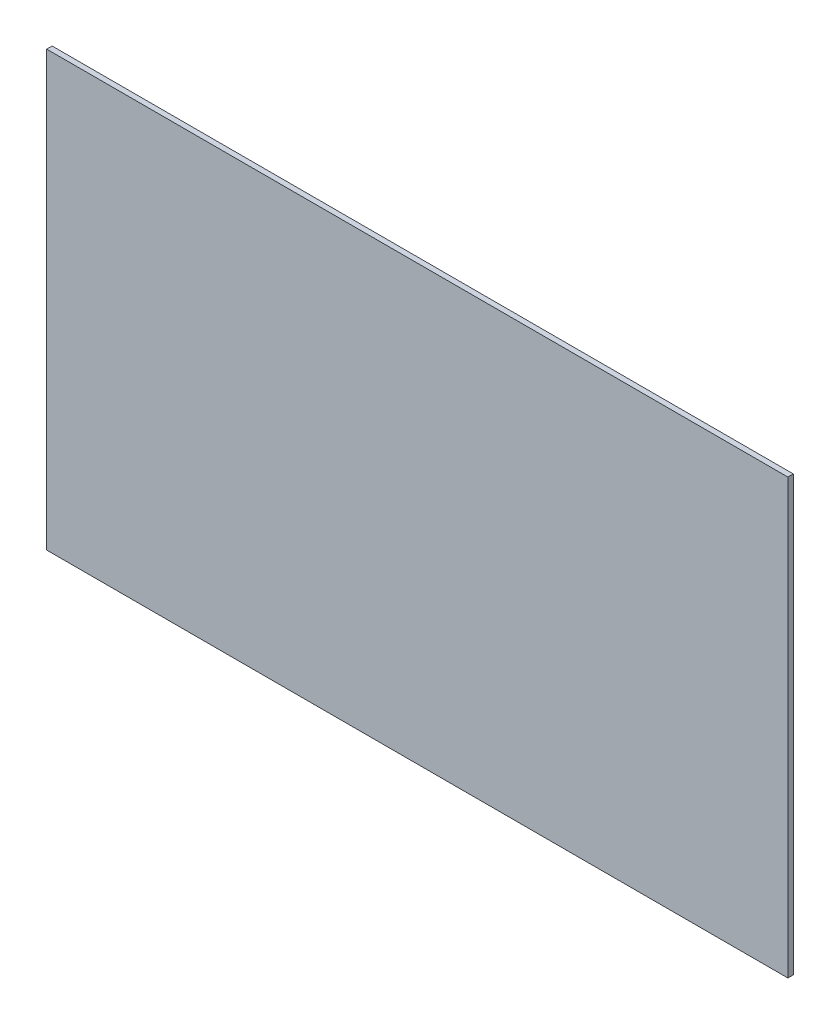
SolidWorks part; units mm, degrees
material "Acrylic (Medium-high impact)"
ref_plane "Front Plane" through (0, 0, 0) normal (0, 0, 1) x (1, 0, 0)
ref_plane "Top Plane" through (0, 0, 0) normal (0, 1, 0) x (1, 0, 0)
ref_plane "Right Plane" through (0, 0, 0) normal (1, 0, 0) x (0, 0, -1)
sketch "Sketch1" plane through (0, 0, 0) normal (0, 0, 1) x (1, 0, 0)
  line L1 (-205, -120) -> (205, -120)
  line L2 (-205, -120) -> (-205, 120)
  line L3 (-205, 120) -> (205, 120)
  line L4 (205, -120) -> (205, 120)
  line L5 (-205, -120) -> (205, 120) construction
  line L6 (-205, 120) -> (205, -120) construction
  point P0 (0, 0)
  dimension "D1" = 240
  dimension "D2" = 410
extrude "Boss-Extrude1" add sketch "Sketch1" along normal mid plane 3
